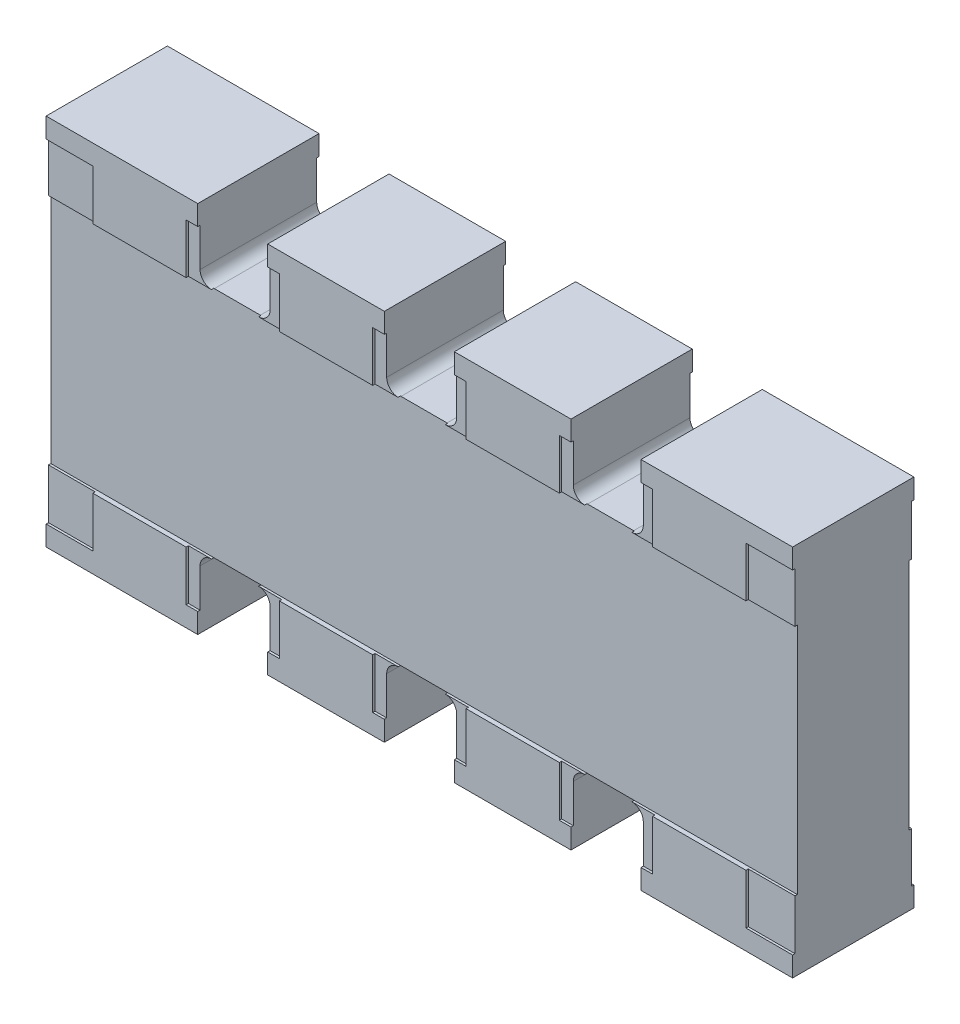
SolidWorks part; units mm, degrees
ref_plane "Front Plane" through (0, 0, 0) normal (0, 0, 1) x (1, 0, 0)
ref_plane "Top Plane" through (0, 0, 0) normal (0, 1, 0) x (1, 0, 0)
ref_plane "Right Plane" through (0, 0, 0) normal (1, 0, 0) x (0, 0, -1)
sketch "Sketch1" plane through (0, 0, 0) normal (0, 0, 1) x (1, 0, 0)
  line L1 (-1.6, 0.8) -> (1.6, 0.8)
  line L2 (-1.6, 0.8) -> (-1.6, -0.8)
  line L3 (-1.6, -0.8) -> (1.6, -0.8)
  line L4 (1.6, 0.8) -> (1.6, -0.8)
  line L5 (-1.6, 0.8) -> (1.6, -0.8) construction
  line L6 (-1.6, -0.8) -> (1.6, 0.8) construction
  point P0 (0, 0)
  dimension "D1" = 3.2
  dimension "D2" = 1.6
extrude "Boss-Extrude1" add sketch "Sketch1" along normal blind 0.5
sketch "Sketch2" plane through (0, 0, 0) normal (0, 0, -1) x (-1, 0, 0)
  line L0 (0, 0.8) -> (0, -0.8) construction
  line L1 (-1.6, 0.8) -> (1.6, 0.8) construction
  line L2 (1.6, -0.8) -> (-1.6, -0.8) construction
  line L3 (-1.6, 0) -> (1.6, 0) construction
  line L4 (-1.6, -0.8) -> (-1.6, 0.8) construction
  line L5 (1.6, 0.8) -> (1.6, -0.8) construction
  line L6 (-0.4, 0.8) -> (-0.4, -0.8) construction
  line L7 (-1.6, 0.5) -> (1.6, 0.5) construction
  line L8 (-0.15, 0.8) -> (0.15, 0.8)
  line L9 (-0.65, 0.8) -> (-0.65, 0.55)
  line L10 (-0.15, 0.8) -> (-0.15, 0.55)
  line L11 (0.95, 0.8) -> (0.65, 0.8)
  line L12 (-1.2, 0.9486) -> (-1.2, 0.0626) construction
  line L13 (-0.95, 0.8) -> (-0.95, 0.55)
  line L14 (-1.45, 0.8) -> (-1.45, 0.55) [skipped]
  line L15 (0.8986, 0.5) -> (0.7014, 0.5)
  line L17 (-0.8986, 0.5) -> (-0.7014, 0.5)
  line L18 (-0.0986, 0.5) -> (0.0986, 0.5)
  line L19 (-0.95, 0.8) -> (-0.65, 0.8)
  line L20 (0.95, 0.8) -> (0.95, 0.55)
  line L21 (0.15, 0.8) -> (0.15, 0.55)
  line L22 (0.65, 0.8) -> (0.65, 0.55)
  line L23 (0.65, -0.8) -> (0.65, -0.55)
  line L24 (0.15, -0.8) -> (0.15, -0.55)
  line L25 (0.95, -0.8) -> (0.95, -0.55)
  line L26 (-0.95, -0.8) -> (-0.65, -0.8)
  line L27 (-0.0986, -0.5) -> (0.0986, -0.5)
  line L28 (-0.8986, -0.5) -> (-0.7014, -0.5)
  line L29 (0.8986, -0.5) -> (0.7014, -0.5)
  line L30 (-0.95, -0.8) -> (-0.95, -0.55)
  line L31 (0.95, -0.8) -> (0.65, -0.8)
  line L32 (-0.15, -0.8) -> (-0.15, -0.55)
  line L33 (-0.65, -0.8) -> (-0.65, -0.55)
  line L34 (-0.15, -0.8) -> (0.15, -0.8)
  arc A0 (-0.65, 0.55) -> (-0.7014, 0.5) centre (-0.7, 0.55) cw
  arc A1 (-0.15, 0.55) -> (-0.0986, 0.5) centre (-0.1, 0.55) ccw
  arc A2 (0.95, 0.55) -> (0.8986, 0.5) centre (0.9, 0.55) cw
  arc A3 (-0.95, 0.55) -> (-0.8986, 0.5) centre (-0.9, 0.55) ccw
  arc A4 (-1.45, 0.55) -> (-1.5014, 0.5) centre (-1.5, 0.55) cw [skipped]
  arc A5 (0.15, 0.55) -> (0.0986, 0.5) centre (0.1, 0.55) cw
  arc A6 (0.65, 0.55) -> (0.7014, 0.5) centre (0.7, 0.55) ccw
  arc A7 (0.65, -0.55) -> (0.7014, -0.5) centre (0.7, -0.55) cw
  arc A8 (0.15, -0.55) -> (0.0986, -0.5) centre (0.1, -0.55) ccw
  arc A9 (-0.95, -0.55) -> (-0.8986, -0.5) centre (-0.9, -0.55) cw
  arc A10 (0.95, -0.55) -> (0.8986, -0.5) centre (0.9, -0.55) ccw
  arc A11 (-0.15, -0.55) -> (-0.0986, -0.5) centre (-0.1, -0.55) cw
  arc A12 (-0.65, -0.55) -> (-0.7014, -0.5) centre (-0.7, -0.55) ccw
  point P50 (0, 0.5)
  point P75 (0, -0.5)
  dimension "D4" = 2
  dimension "D1" = 0.4
  dimension "D2" = 0.3
  dimension "D3" = 0.25
  dimension "D5" = 0.8
extrude "Cut-Extrude1" cut sketch "Sketch2" against normal through all
sketch "Sketch3" plane through (0, 0, 0) normal (0, 0, -1) x (-1, 0, 0)
  line L0 (-1.6, 0.5) -> (1.6, 0.5) construction
  line L1 (-1.6, -0.8) -> (-1.6, 0.8) construction
  line L2 (1.6, 0.8) -> (1.6, -0.8) construction
  line L3 (-1.6, -0.5) -> (1.6, -0.5) construction
  line L5 (-1.6, 0.5) -> (1.6, 0.5)
  line L6 (-1.6, 0.5) -> (-1.6, -0.5)
  line L7 (-1.6, -0.5) -> (1.6, -0.5)
  line L8 (1.6, 0.5) -> (1.6, -0.5)
extrude "Cut-Extrude2" cut sketch "Sketch3" against normal blind 0.01
ref_plane "Plane1" through (0, 0, 0.25) normal (0, 0, -1) x (-1, 0, 0)
mirror "Mirror1" about plane through (0, 0, 0.25) normal (0, 0, -1) of "Cut-Extrude2"
sketch "Sketch4" plane through (0, 0, 0) normal (0, 0, -1) x (-1, 0, 0)
  line L0 (0, 0.5) -> (0, -0.5) construction
  line L1 (0.0986, 0.5) -> (-0.0986, 0.5) construction
  line L2 (-0.0986, -0.5) -> (0.0986, -0.5) construction
  line L3 (-1.6, 0) -> (1.6, 0) construction
  line L4 (-1.6, 0.5) -> (-1.6, -0.5) construction
  line L5 (1.6, -0.5) -> (1.6, 0.5) construction
  line L6 (-0.4, 0.8) -> (-0.4, 0) construction
  line L7 (-0.65, 0.8) -> (-0.15, 0.8) construction
  line L8 (-0.65, 0.7145) -> (-0.6, 0.7145)
  line L10 (-0.65, 0.55) -> (-0.65, 0.8) construction
  line L11 (-0.6, 0.7145) -> (-0.6, 0.5)
  line L12 (-0.1014, 0.5) -> (-0.6986, 0.5) construction
  line L13 (-0.65, 0.7145) -> (-0.65, 0.8)
  line L14 (-0.65, 0.8) -> (-0.15, 0.8)
  line L15 (-0.15, 0.7145) -> (-0.15, 0.8)
  line L16 (-0.2, 0.7145) -> (-0.2, 0.5)
  line L17 (-0.15, 0.7145) -> (-0.2, 0.7145)
  line L18 (-0.6, 0.5) -> (-0.2, 0.5)
  line L19 (-1.45, 0.7145) -> (-1.4, 0.7145)
  line L20 (-1.4, 0.7145) -> (-1.4, 0.5)
  line L21 (-1.45, 0.8) -> (-1.6, 0.8)
  line L22 (-1.45, 0.8) -> (-0.95, 0.8)
  line L23 (-0.95, 0.7145) -> (-0.95, 0.8)
  line L24 (-1, 0.7145) -> (-1, 0.5)
  line L25 (-0.95, 0.7145) -> (-1, 0.7145)
  line L26 (-1.4, 0.5) -> (-1, 0.5)
  line L27 (1.6, 0.8) -> (1.6, 0.7145)
  line L28 (1.45, 0.7145) -> (1.6, 0.7145)
  line L29 (1.4, 0.5) -> (1, 0.5)
  line L30 (0.95, 0.7145) -> (1, 0.7145)
  line L31 (1, 0.7145) -> (1, 0.5)
  line L32 (0.95, 0.7145) -> (0.95, 0.8)
  line L33 (1.45, 0.8) -> (0.95, 0.8)
  line L34 (1.45, 0.8) -> (1.6, 0.8)
  line L35 (0.6, 0.5) -> (0.2, 0.5)
  line L36 (0.15, 0.7145) -> (0.2, 0.7145)
  line L37 (0.2, 0.7145) -> (0.2, 0.5)
  line L38 (0.15, 0.7145) -> (0.15, 0.8)
  line L39 (0.65, 0.8) -> (0.15, 0.8)
  line L40 (0.65, 0.7145) -> (0.65, 0.8)
  line L41 (0.6, 0.7145) -> (0.6, 0.5)
  line L42 (0.65, 0.7145) -> (0.6, 0.7145)
  line L43 (-1.45, 0.7145) -> (-1.45, 0.8) [skipped]
  line L44 (-1.45, 0.7145) -> (-1.6, 0.7145)
  line L45 (-1.6, 0.5) -> (-1.6, 0.8) construction
  line L46 (-1.6, 0.8) -> (-1.6, 0.7145)
  line L47 (1.4, 0.7145) -> (1.4, 0.5)
  line L48 (1.45, 0.7145) -> (1.4, 0.7145)
  line L49 (1.45, -0.7145) -> (1.4, -0.7145)
  line L50 (1.4, -0.7145) -> (1.4, -0.5)
  line L51 (-1.6, -0.8) -> (-1.6, -0.7145)
  line L52 (-1.45, -0.7145) -> (-1.6, -0.7145)
  line L53 (0.65, -0.7145) -> (0.6, -0.7145)
  line L54 (0.6, -0.7145) -> (0.6, -0.5)
  line L55 (0.65, -0.7145) -> (0.65, -0.8)
  line L56 (0.65, -0.8) -> (0.15, -0.8)
  line L57 (0.15, -0.7145) -> (0.15, -0.8)
  line L58 (0.2, -0.7145) -> (0.2, -0.5)
  line L59 (0.15, -0.7145) -> (0.2, -0.7145)
  line L60 (0.6, -0.5) -> (0.2, -0.5)
  line L61 (1.45, -0.8) -> (1.6, -0.8)
  line L62 (1.45, -0.8) -> (0.95, -0.8)
  line L63 (0.95, -0.7145) -> (0.95, -0.8)
  line L64 (1, -0.7145) -> (1, -0.5)
  line L65 (0.95, -0.7145) -> (1, -0.7145)
  line L66 (1.4, -0.5) -> (1, -0.5)
  line L67 (1.45, -0.7145) -> (1.6, -0.7145)
  line L68 (1.6, -0.8) -> (1.6, -0.7145)
  line L69 (-1.4, -0.5) -> (-1, -0.5)
  line L70 (-0.95, -0.7145) -> (-1, -0.7145)
  line L71 (-1, -0.7145) -> (-1, -0.5)
  line L72 (-0.95, -0.7145) -> (-0.95, -0.8)
  line L73 (-1.45, -0.8) -> (-0.95, -0.8)
  line L74 (-1.45, -0.8) -> (-1.6, -0.8)
  line L75 (-1.4, -0.7145) -> (-1.4, -0.5)
  line L76 (-1.45, -0.7145) -> (-1.4, -0.7145)
  line L77 (-0.6, -0.5) -> (-0.2, -0.5)
  line L78 (-0.15, -0.7145) -> (-0.2, -0.7145)
  line L79 (-0.2, -0.7145) -> (-0.2, -0.5)
  line L80 (-0.15, -0.7145) -> (-0.15, -0.8)
  line L81 (-0.65, -0.8) -> (-0.15, -0.8)
  line L82 (-0.65, -0.7145) -> (-0.65, -0.8)
  line L83 (-0.6, -0.7145) -> (-0.6, -0.5)
  line L84 (-0.65, -0.7145) -> (-0.6, -0.7145)
  dimension "D1" = 0.05
  dimension "D2" = 2
extrude "Boss-Extrude2" add sketch "Sketch4" along normal blind 0.01
mirror "Mirror2" about plane through (0, 0, 0.25) normal (0, 0, -1) of "Boss-Extrude2"
sketch "Sketch5" plane through (0, 0, 0.01) normal (0, 0, -1) x (-1, 0, 0)
  line L0 (-1.6, -0.1976) -> (1.6, -0.1976) construction
  line L1 (-1.6, 0.5) -> (-1.6, -0.5) construction
  line L2 (1.6, -0.5) -> (1.6, 0.5) construction
  text T0 "<b>EXB38V  </b>" font "Tahoma" height 0.5
extrude "Boss-Extrude3" [suppressed] add sketch "Sketch5" along normal blind 0.01
